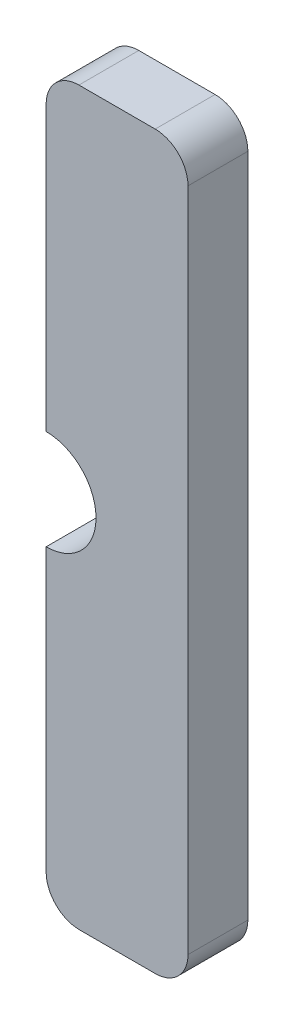
SolidWorks part; units mm, degrees
ref_plane "Спереди" through (0, 0, 0) normal (0, 0, 1) x (1, 0, 0)
ref_plane "Сверху" through (0, 0, 0) normal (0, 1, 0) x (1, 0, 0)
ref_plane "Справа" through (0, 0, 0) normal (1, 0, 0) x (0, 0, -1)
ref_plane "Плоскость1" through (0, 0, 0) normal (0, 0, -1) x (-1, 0, 0)
sketch "Эскиз1" plane through (0, 0, 0) normal (0, 0, -1) x (-1, 0, 0)
  line L0 (-32.4, 25.4) -> (-29.75, 25.4)
  line L1 (-28.575, 26.5836) -> (-28.575, 36.4502)
  line L3 (-28.575, 39.9502) -> (-28.575, 49.9084)
  line L4 (-29.725, 51.05) -> (-32.4, 51.05)
  line L5 (-33.55, 49.9) -> (-33.55, 26.55)
  arc A0 (-29.75, 25.4) -> (-28.575, 26.5836) centre (-29.7495, 26.5745) ccw
  arc A3 (-28.575, 49.9084) -> (-29.725, 51.05) centre (-29.7256, 49.8994) ccw
  arc A4 (-32.4, 51.05) -> (-33.55, 49.9) centre (-32.3994, 49.8994) ccw
  arc A5 (-33.55, 26.55) -> (-32.4, 25.4) centre (-32.3994, 26.5506) ccw
  arc A6 (-28.575, 39.9502) -> (-28.575, 36.4502) centre (-28.575, 38.2002) ccw
extrude "Бобышка-Вытянуть1" add sketch "Эскиз1" against normal blind 2.1
